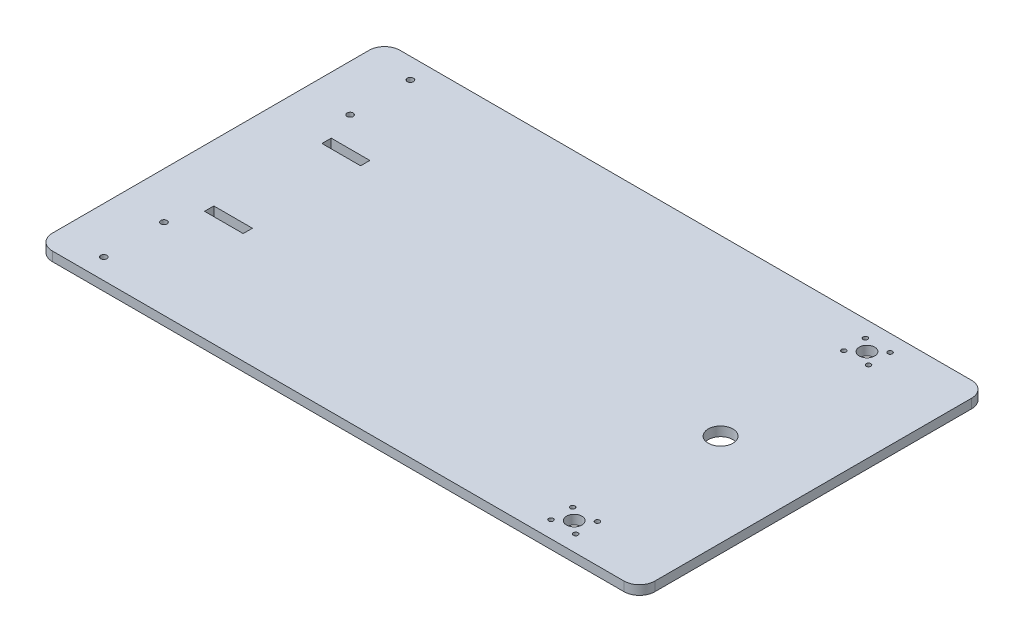
SolidWorks part; units mm, degrees
ref_plane "Front Plane" through (0, 0, 0) normal (0, 0, 1) x (1, 0, 0)
ref_plane "Top Plane" through (0, 0, 0) normal (0, 1, 0) x (1, 0, 0)
ref_plane "Right Plane" through (0, 0, 0) normal (1, 0, 0) x (0, 0, -1)
sketch "Sketch1" plane through (0, 0, 0) normal (0, 1, 0) x (1, 0, 0)
  line L0 (-195, 0) -> (195, 0) construction
  line L1 (-185, 112.5) -> (185, 112.5)
  line L2 (-195, 102.5) -> (-195, -102.5)
  line L4 (195, 102.5) -> (195, -102.5)
  line L5 (-195, 112.5) -> (195, -112.5) construction
  line L6 (-195, -112.5) -> (195, 112.5) construction
  line L7 (195, 0) -> (135, 0) construction
  line L8 (121.75, -109.5) -> (148.25, -109.5) construction
  line L9 (135, -80) -> (135, -109.5) construction
  line L10 (135, -44.5) -> (147.5, -44.5) construction
  line L11 (135, -44.5) -> (122.5, -44.5) construction
  line L12 (122.5, -44.5) -> (122.5, -112.5) construction
  line L13 (147.5, -44.5) -> (147.5, -112.5) construction
  line L14 (147.5, 44.5) -> (147.5, 112.5) construction
  line L15 (135, 44.5) -> (122.5, 44.5) construction
  line L16 (135, 44.5) -> (147.5, 44.5) construction
  line L17 (122.5, 44.5) -> (122.5, 112.5) construction
  line L18 (135, -112.5) -> (135, -150) construction
  line L19 (102.5, -150) -> (167.5, -150) construction
  line L20 (167.5, -150) -> (167.5, -112.5) construction
  line L21 (102.5, -150) -> (102.5, -112.5) construction
  line L22 (167.5, 150) -> (167.5, 112.5) construction
  line L23 (135, 112.5) -> (135, 150) construction
  line L24 (102.5, 150) -> (167.5, 150) construction
  line L25 (102.5, 150) -> (102.5, 112.5) construction
  line L26 (-195, 0) -> (-165, 0) construction
  line L27 (-165, 0) -> (-165, -112.5) construction
  line L28 (-165, -112.5) -> (-165, -56.25) construction
  line L29 (-165, -56.25) -> (-165, -103.25) construction
  line L30 (-181, -103.25) -> (-149, -103.25) construction
  line L31 (-149, -103.25) -> (-149, -56.25) construction
  line L32 (-149, -56.25) -> (-181, -56.25) construction
  line L33 (-181, -103.25) -> (-181, -56.25) construction
  line L34 (-181, 103.25) -> (-149, 103.25) construction
  line L35 (-181, 103.25) -> (-181, 56.25) construction
  line L36 (-149, 56.25) -> (-181, 56.25) construction
  line L37 (-149, 103.25) -> (-149, 56.25) construction
  line L38 (-165, 0) -> (-165, 112.5) construction
  line L39 (-195, 0) -> (-165, 0) construction
  line L40 (-165, 0) -> (-145, 0) construction
  line L41 (-165, 41) -> (-158, 41) construction
  line L42 (-165, 41) -> (-125, 41) construction
  line L43 (-165, 41) -> (-165, -41) construction
  line L44 (-165, -41) -> (-125, -41) construction
  line L45 (-125, 41) -> (-125, -41) construction
  line L46 (-165, 41) -> (-125, -41) construction
  line L47 (-165, -41) -> (-125, 41) construction
  line L48 (-158, 41) -> (-158, 35)
  line L49 (-158, 35) -> (-133, 35)
  line L50 (-133, 35) -> (-133, 41)
  line L51 (-133, 41) -> (-158, 41)
  line L52 (-133, -35) -> (-133, -41)
  line L53 (-158, -35) -> (-133, -35)
  line L54 (-133, -41) -> (-158, -41)
  line L55 (-158, -41) -> (-158, -35)
  line L56 (121.75, -112.5) -> (148.25, -112.5) construction
  line L57 (121.75, -112.5) -> (121.75, -80) construction
  line L58 (121.75, -80) -> (148.25, -80) construction
  line L59 (148.25, -80) -> (148.25, -112.5) construction
  line L60 (-185, -112.5) -> (185, -112.5)
  line L61 (135, -94.75) -> (135, -87.75) construction
  line L62 (121.75, -112.5) -> (121.75, -109.5) construction
  line L63 (127, -87.75) -> (143, -87.75) construction
  line L64 (143, -87.75) -> (143, -101.75) construction
  line L65 (143, -101.75) -> (127, -101.75) construction
  line L66 (127, -87.75) -> (127, -101.75) construction
  line L67 (127, 87.75) -> (127, 101.75) construction
  line L68 (143, 87.75) -> (143, 101.75) construction
  line L69 (127, 87.75) -> (143, 87.75) construction
  line L70 (135, 80) -> (135, 109.5) construction
  line L71 (143, 101.75) -> (127, 101.75) construction
  line L72 (148.25, 80) -> (148.25, 112.5) construction
  line L73 (121.75, 109.5) -> (148.25, 109.5) construction
  line L74 (121.75, 112.5) -> (121.75, 80) construction
  line L75 (121.75, 80) -> (148.25, 80) construction
  line L76 (135, 112.5) -> (135, -112.5) construction
  line L77 (-165, -103.25) -> (-165, -99.25) construction
  line L78 (-165, -56.25) -> (-165, -60.25) construction
  arc A0 (-185, 112.5) -> (-195, 102.5) centre (-185, 102.5) ccw
  arc A1 (-195, -102.5) -> (-185, -112.5) centre (-185, -102.5) ccw
  arc A2 (185, -112.5) -> (195, -102.5) centre (185, -102.5) ccw
  arc A3 (185, 112.5) -> (195, 102.5) centre (185, 102.5) cw
  circle A4 centre (135, 0) radius 8
  circle A5 centre (135, -94.75) radius 5
  circle A6 centre (143, -87.75) radius 1.5
  circle A7 centre (143, -101.75) radius 1.5
  circle A8 centre (127, -87.75) radius 1.5
  circle A9 centre (127, -101.75) radius 1.5
  circle A10 centre (143, 101.75) radius 1.5
  circle A11 centre (143, 87.75) radius 1.5
  circle A12 centre (127, 101.75) radius 1.5
  circle A13 centre (127, 87.75) radius 1.5
  circle A14 centre (135, 94.75) radius 5
  circle A15 centre (-165, -60.25) radius 2
  circle A16 centre (-165, -99.25) radius 2
  circle A17 centre (-165, 60.25) radius 2
  circle A18 centre (-165, 99.25) radius 2
  point P0 (0, 0)
  point P73 (135, -112.5)
  point P90 (135, -101.75)
  dimension "D4" = 10
  dimension "D20" = 16
  dimension "D1" = 390
  dimension "D2" = 225
  dimension "D3" = 60
  dimension "D5" = 300
  dimension "D6" = 37.5
  dimension "D7" = 47
  dimension "D8" = 32
  dimension "D9" = 30
  dimension "D10" = 65
  dimension "D11" = 25
  dimension "D12" = 47.5
  dimension "D13" = 44.5
  dimension "D14" = 82
  dimension "D15" = 40
  dimension "D16" = 50
  dimension "D17" = 6
  dimension "D18" = 25
  dimension "D19" = 7
  dimension "D21" = 26.5
extrude "Boss-Extrude1" add sketch "Sketch1" along normal blind 6
